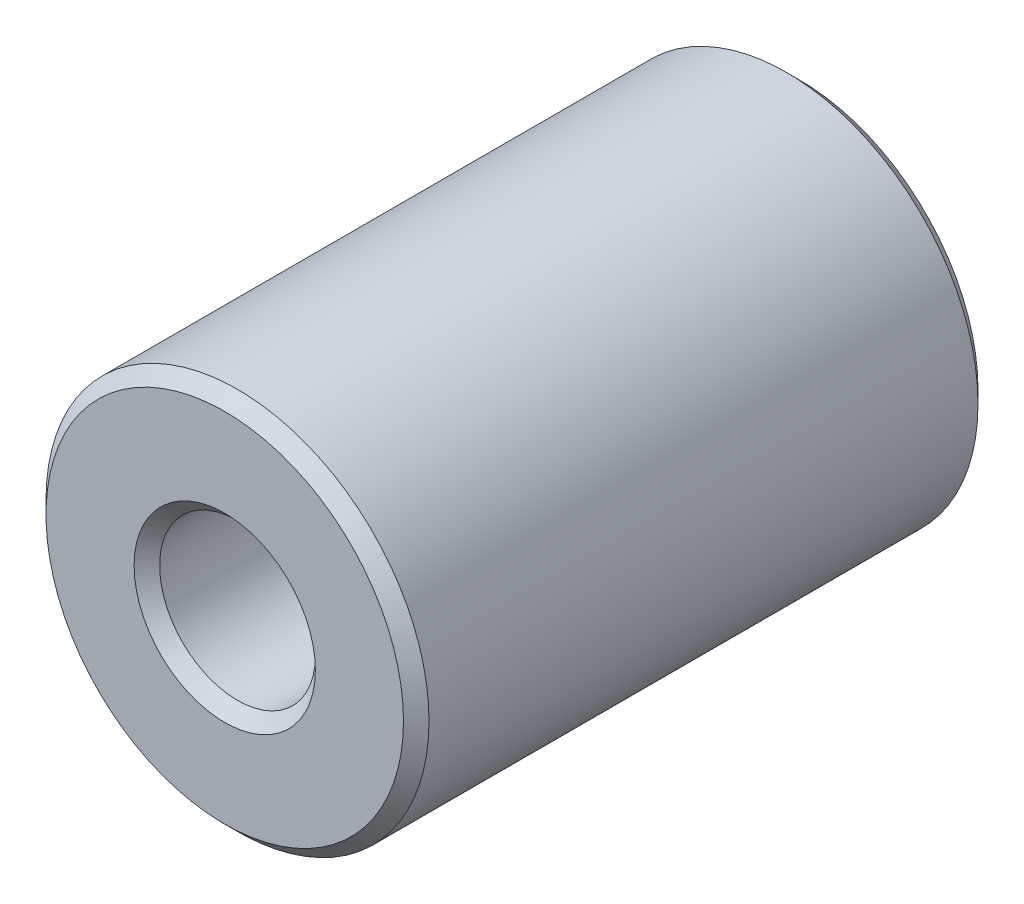
SolidWorks part; units mm, degrees
material "1.0037 (S235JR)"
ref_plane "Płaszczyzna przednia" through (0, 0, 0) normal (0, 0, 1) x (1, 0, 0)
ref_plane "Płaszczyzna górna" through (0, 0, 0) normal (0, 1, 0) x (1, 0, 0)
ref_plane "Płaszczyzna prawa" through (0, 0, 0) normal (1, 0, 0) x (0, 0, -1)
sketch "Szkic1" plane through (0, 0, 0) normal (0, 0, 1) x (1, 0, 0)
  circle A0 centre (0, 0) radius 15
  circle A1 centre (0, 0) radius 6.1
  dimension "D1" = 30
  dimension "D2" = 12.2
extrude "Dodanie-wyciągnięcie1" add sketch "Szkic1" along normal blind 45
chamfer "Sfazowanie1" distance 1 angle 45 4 edges at (15, 0, 0) (15, 0, 45) (6.1, 0, 0) (6.1, 0, 45)
